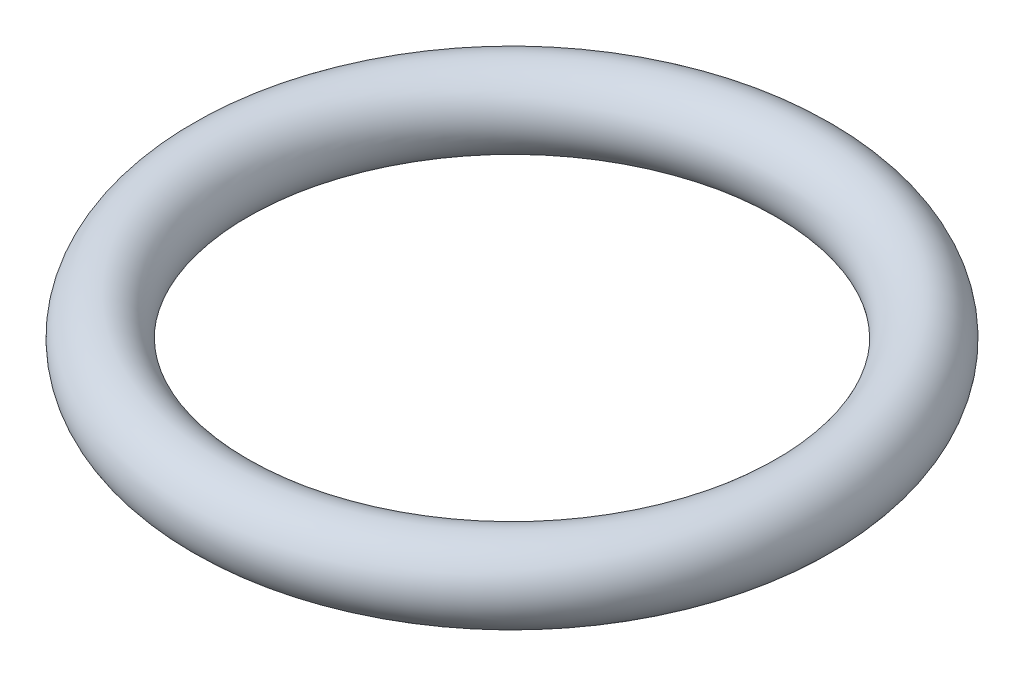
SolidWorks part; units mm, degrees
ref_plane "Front" through (0, 0, 0) normal (0, 0, 1) x (1, 0, 0)
ref_plane "Top" through (0, 0, 0) normal (0, 1, 0) x (1, 0, 0)
ref_plane "Right" through (0, 0, 0) normal (1, 0, 0) x (0, 0, -1)
sketch "Sketch2" plane through (0, 0, 0) normal (0, 0, 1) x (1, 0, 0)
  line L0 (0, 7.0164) -> (0, -9.4885) construction
  line L1 (0, 0) -> (19, 0) construction
  circle A0 centre (19, 0) radius 2.5
  dimension "D1" = 5
  dimension "D2" = 19
revolve "Revolve1" add sketch "Sketch2" angle 360 about L0
